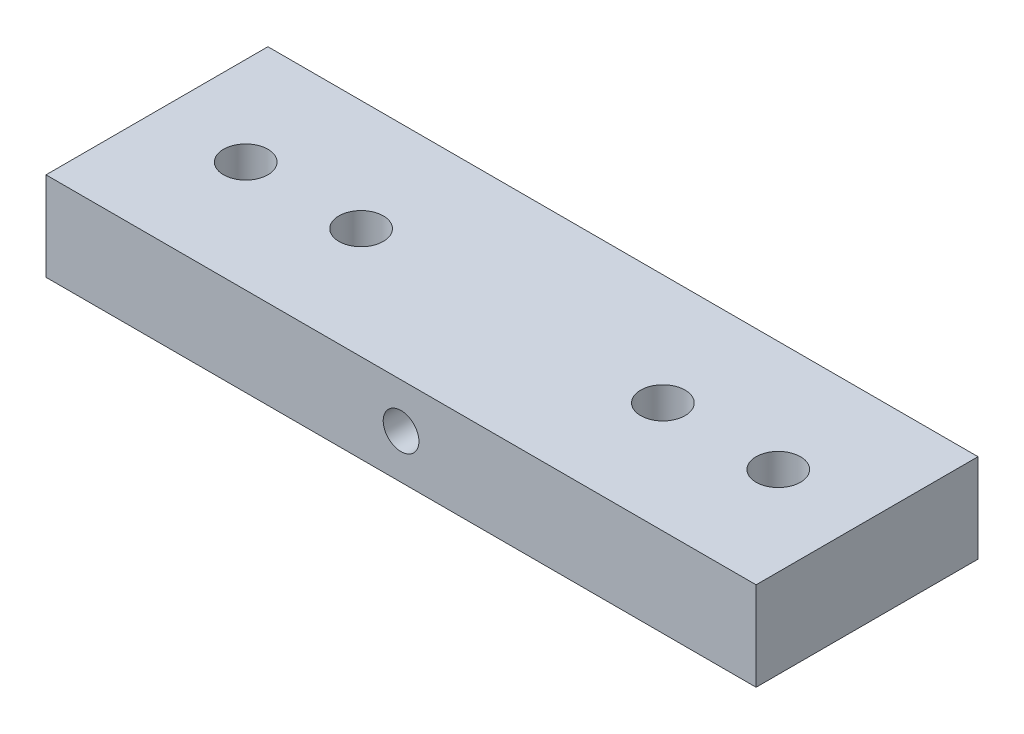
SolidWorks part; units mm, degrees
ref_plane "Front Plane" through (0, 0, 0) normal (0, 0, 1) x (1, 0, 0)
ref_plane "Top Plane" through (0, 0, 0) normal (0, 1, 0) x (1, 0, 0)
ref_plane "Right Plane" through (0, 0, 0) normal (1, 0, 0) x (0, 0, -1)
sketch "Sketch1" plane through (0, 0, 0) normal (0, 1, 0) x (1, 0, 0)
  line L0 (19.386, 0) -> (19.386, 31.75) construction
  line L1 (-31.414, 0) -> (70.186, 0)
  line L2 (-31.414, 0) -> (-31.414, 31.75)
  line L3 (-31.414, 31.75) -> (70.186, 31.75)
  line L4 (70.186, 0) -> (70.186, 31.75)
  circle A0 centre (-18.714, 15.875) radius 3.175
  circle A1 centre (57.486, 15.875) radius 3.175
  circle A3 centre (-2.204, 15.875) radius 3.175
  circle A4 centre (40.976, 15.875) radius 3.175
  point P8 (-31.414, 15.875)
  dimension "D3" = 6.35
  dimension "D4" = 38.1
  dimension "D5" = 6.35
  dimension "D6" = 21.59
  dimension "D1" = 101.6
  dimension "D2" = 31.75
extrude "Boss-Extrude1" add sketch "Sketch1" along normal blind 12.7
sketch "Sketch3" plane through (0, 0, 0) normal (0, 0, 1) x (1, 0, 0)
  line L0 (-31.414, 12.7) -> (-31.414, 0) construction
  line L1 (-31.414, 0) -> (70.186, 0) construction
  circle A0 centre (19.386, 6.35) radius 3.175
  dimension "D1" = 6.35
  dimension "D3" = 6.35
  dimension "D2" = 50.8
hole_wizard "1/4-20 Tapped Hole1" positions "3DSketch1" profile "Sketch4" tap size "1/4-20" standard "ANSI Inch" end condition through all
sketch3d "3DSketch1"
  point P0 (19.386, 6.35, 0)
sketch "Sketch4" plane through (19.386, 6.35, 0) normal (1, 0, 0) x (0, -1, 0)
  line L0 (0, 0) -> (0, 31.75)
  line L1 (0, 31.75) -> (2.5527, 31.75)
  line L2 (2.5527, 31.75) -> (2.5527, 0)
  line L5 (2.5527, 0) -> (0, 0)
  line L11 (0, -6.35) -> (0, 107.95) construction
  dimension "Thru Tap Drill Dia." = 5.1054
  dimension "Thru Tap Drill Depth" = 31.75
cosmetic thread "Hole Thread1" parameters "D2"=6.35
